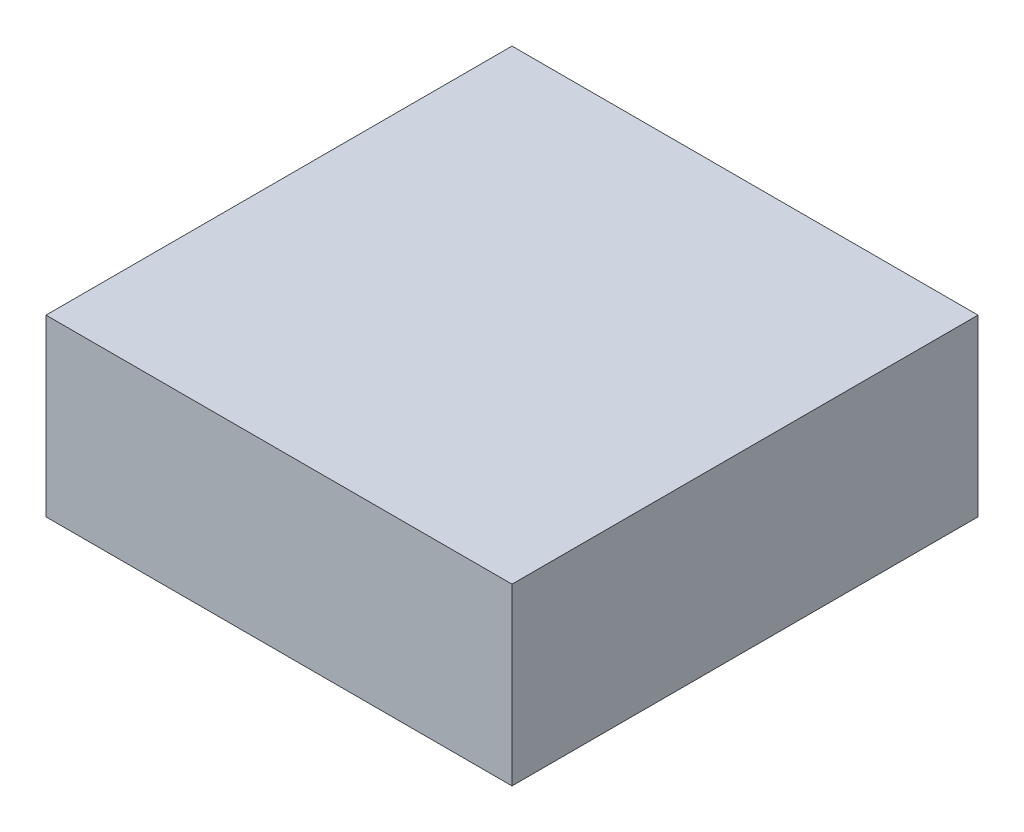
SolidWorks part; units mm, degrees
ref_plane "Front Plane" through (0, 0, 0) normal (0, 0, 1) x (1, 0, 0)
ref_plane "Top Plane" through (0, 0, 0) normal (0, 1, 0) x (1, 0, 0)
ref_plane "Right Plane" through (0, 0, 0) normal (1, 0, 0) x (0, 0, -1)
sketch "Sketch1" plane through (0, 0, 0) normal (0, 1, 0) x (1, 0, 0)
  circle A0 centre (0, 0) radius 7315.2 construction
  circle A1 centre (0, 0) radius 6096 construction
  dimension "D1" = 14630.4
  dimension "D2" = 12192
sketch "Sketch2" plane through (0, 0, 0) normal (0, 0, 1) x (1, 0, 0)
  line L2 (-7315.2, 0) -> (7315.2, 0) construction
  arc A0 (7315.2, 0) -> (-7315.2, 0) centre (0, 0) ccw construction
  arc A1 (6096, 0) -> (-6096, 0) centre (0, 0) ccw construction
  dimension "D1" = 14630.4
  dimension "D2" = 12192
sketch "Sketch3" plane through (0, 0, 0) normal (0, 1, 0) x (1, 0, 0)
  line L1 (-609.6, -609.6) -> (609.6, -609.6)
  line L2 (-609.6, -609.6) -> (-609.6, 609.6)
  line L3 (-609.6, 609.6) -> (609.6, 609.6)
  line L4 (609.6, -609.6) -> (609.6, 609.6)
  line L5 (0, 609.6) -> (0, -609.6) construction
  line L6 (-609.6, 0) -> (609.6, 0) construction
  point P0 (0, 0)
  dimension "D1" = 1219.2
  dimension "D2" = 1219.2
extrude "Boss-Extrude1" add sketch "Sketch3" along normal blind 457.2
sketch "Sketch4" plane through (0, 457.2, 0) normal (0, 1, 0) x (1, 0, 0)
  line L0 (0, 609.6) -> (0, -659.8805) construction
  line L1 (609.6, 609.6) -> (-609.6, 609.6) construction
  line L2 (-609.6, 0) -> (609.6, 0) construction
  line L3 (-609.6, 609.6) -> (-609.6, -609.6) construction
  line L4 (609.6, -609.6) -> (609.6, 609.6) construction
  circle A0 centre (0, 0) radius 67.0189 construction
